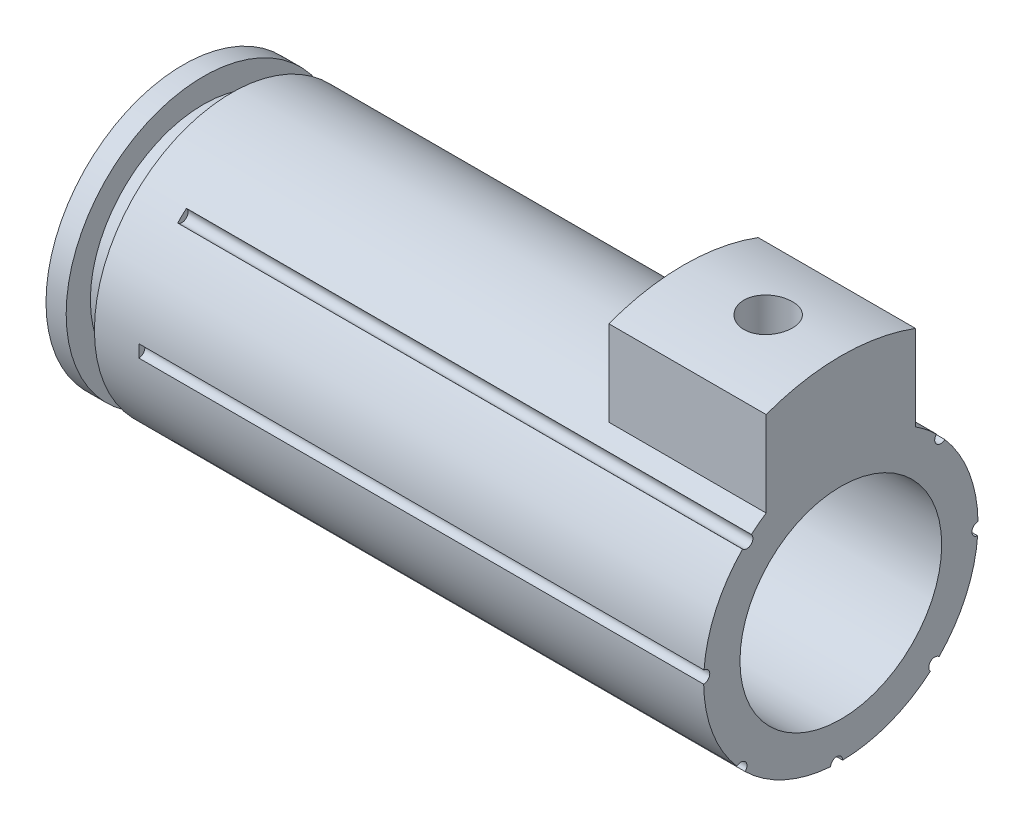
SolidWorks part; units mm, degrees
material "ABS"
ref_plane "Front Plane" through (0, 0, 0) normal (0, 0, 1) x (1, 0, 0)
ref_plane "Top Plane" through (0, 0, 0) normal (0, 1, 0) x (1, 0, 0)
ref_plane "Right Plane" through (0, 0, 0) normal (1, 0, 0) x (0, 0, -1)
sketch "Sketch1" plane through (0, 0, 0) normal (0, 0, 1) x (1, 0, 0)
  line L0 (-78.2418, 0) -> (71.3055, 0) construction
  line L1 (20.701, 0) -> (20.701, 8.636)
  line L2 (20.701, 8.636) -> (-17.653, 8.636)
  line L3 (-20.701, 8.636) -> (-20.701, 0)
  line L4 (-20.701, 0) -> (20.701, 0)
  line L5 (-17.653, 8.636) -> (-17.653, 7.112)
  line L6 (-17.653, 7.112) -> (-19.431, 7.112)
  line L7 (-19.431, 7.112) -> (-19.431, 8.636)
  line L8 (-19.431, 8.636) -> (-20.701, 8.636)
  dimension "D1" = 41.402
  dimension "D2" = 1.27
  dimension "D3" = 1.778
  dimension "D4" = 1.524
  dimension "D5" = 8.636
revolve "Revolve1" add sketch "Sketch1" angle 360 about L0
sketch "Sketch6" plane through (0, 0, 0) normal (0, 1, 0) x (1, 0, 0)
  line L0 (20.701, 0) -> (20.701, 4.699)
  line L1 (20.701, -8.636) -> (20.701, 8.636) construction
  line L2 (20.701, 0) -> (20.701, -4.699)
  line L3 (20.701, -4.699) -> (10.795, -4.699)
  line L4 (10.795, -4.699) -> (10.795, 4.699)
  line L5 (10.795, 4.699) -> (20.701, 4.699)
  dimension "D1" = 4.699
  dimension "D2" = 4.699
  dimension "D3" = 9.906
extrude "Boss-Extrude1" add sketch "Sketch6" along normal blind 13.462
sketch "Sketch7" plane through (20.701, 0, 0) normal (1, 0, 0) x (0, 0, -1)
  circle A0 centre (0, 0) radius 13.462
  dimension "D1" = 26.924
extrude "Cut-Extrude1" cut sketch "Sketch7" against normal blind 13.462 flip side to cut
ref_plane "Plane2" through (0, 13.462, 0) normal (0, 1, 0) x (-1, 0, 0)
sketch "Sketch8" plane through (0, 13.462, 0) normal (0, 1, 0) x (-1, 0, 0)
  circle A0 centre (-16.129, 0) radius 1.524
extrude "Cut-Extrude2" cut sketch "Sketch8" against normal blind 6.35
sketch "Sketch9" plane through (20.701, 0, 0) normal (1, 0, 0) x (0, 0, -1)
  circle A0 centre (0, 0) radius 6.35
  dimension "D1" = 12.7
extrude "Cut-Extrude3" cut sketch "Sketch9" against normal through all
sketch "Sketch10" plane through (20.701, 0, 0) normal (1, 0, 0) x (0, 0, -1)
  circle A0 centre (-5.9163, 6.2911) radius 0.381
  arc A1 (-4.699, 7.2457) -> (4.699, 7.2457) centre (0, 0) ccw construction
  dimension "D1" = 0.762
extrude "Cut-Extrude4" cut sketch "Sketch10" against normal blind 35.56
pattern_circular "CirPattern1" count 8 over 360 about axis through (20.701, 0, 0) along (-1, 0, 0) skipping 1 of "Cut-Extrude4"
